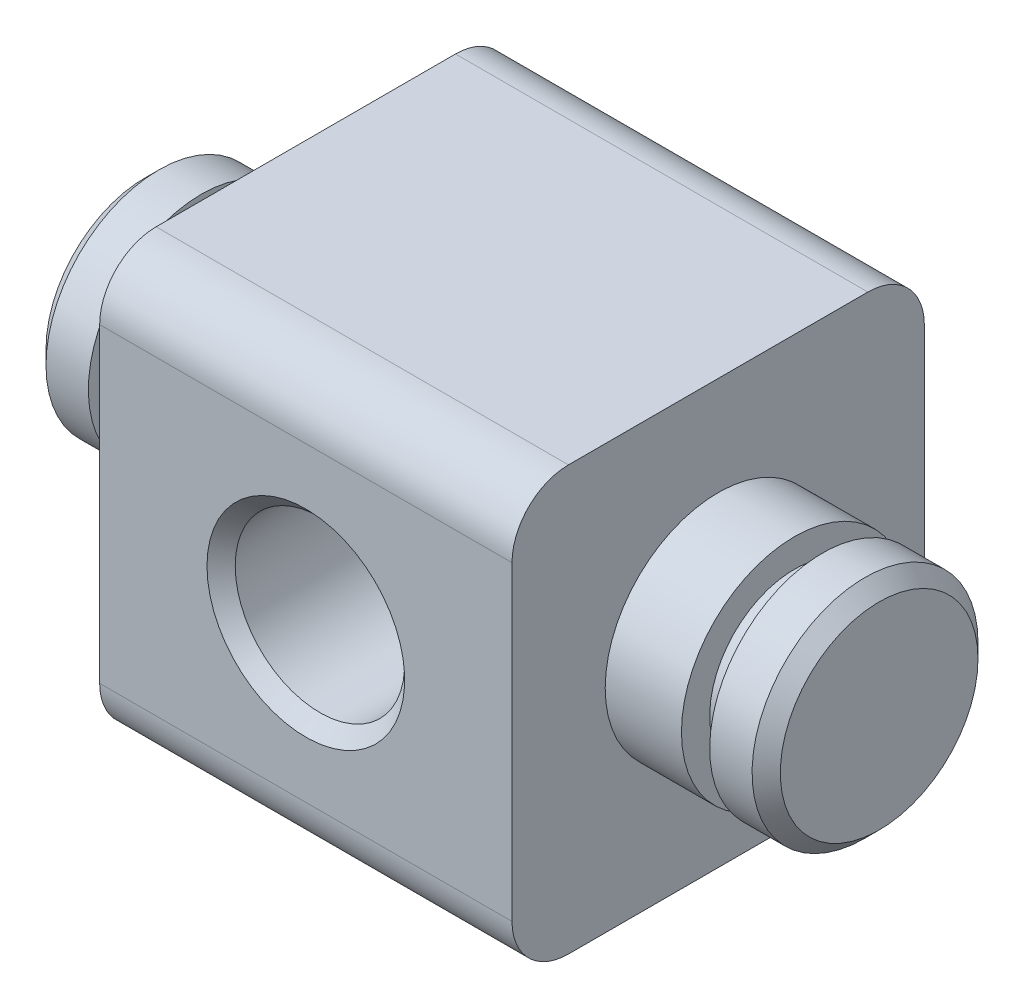
SolidWorks part; units mm, degrees
material "Plain Carbon Steel"
ref_plane "Front Plane" through (0, 0, 0) normal (0, 0, 1) x (1, 0, 0)
ref_plane "Top Plane" through (0, 0, 0) normal (0, 1, 0) x (1, 0, 0)
ref_plane "Right Plane" through (0, 0, 0) normal (1, 0, 0) x (0, 0, -1)
sketch "Sketch1" plane through (0, 0, 0) normal (0, 1, 0) x (1, 0, 0)
  line L1 (7.3, -7.3) -> (-7.3, -7.3)
  line L2 (7.3, -7.3) -> (7.3, 7.3)
  line L3 (7.3, 7.3) -> (-7.3, 7.3)
  line L4 (-7.3, -7.3) -> (-7.3, 7.3)
  line L5 (7.3, -7.3) -> (-7.3, 7.3) construction
  line L6 (7.3, 7.3) -> (-7.3, -7.3) construction
  point P0 (0, 0)
  dimension "D1" = 14.6
extrude "Boss-Extrude1" add sketch "Sketch1" along normal blind 15
sketch "Sketch2" plane through (0, 7.7, -7.3) normal (0, 0, 1) x (1, 0, 0)
  line L0 (-7.3, 7.3) -> (7.3, -7.7) construction
  circle A0 centre (0, -0.2) radius 3
  dimension "D1" = 6
extrude "Cut-Extrude1" cut sketch "Sketch2" along normal through all both and the other way through all from surface contours A0
chamfer "Chamfer1" distance 0.5 angle 45 2 edges at (3, 7.5, -7.3) (3, 7.5, 7.3)
sketch "Sketch3" plane through (-7.3, 0, 0) normal (-1, 0, 0) x (0, 0, 1)
  line L0 (-7.3, 0) -> (7.3, 15) construction
  circle A0 centre (0, 7.5) radius 4
  dimension "D1" = 8
extrude "Boss-Extrude2" add sketch "Sketch3" along normal blind 5.7
sketch "Sketch4" plane through (0, 0, 0) normal (0, 0, 1) x (1, 0, 0)
  line L0 (-13, 7.5) -> (7.3, 7.5) construction
  line L1 (-11, 12.2783) -> (-10, 12.2783)
  line L2 (-11, 12.2783) -> (-11, 10.5)
  line L3 (-11, 10.5) -> (-10, 10.5)
  line L4 (-10, 12.2783) -> (-10, 10.5)
  line L5 (-13, 11.5) -> (-13, 3.5) construction
  line L6 (7.3, 15) -> (7.3, 0) construction
  dimension "D1" = 1
  dimension "D2" = 3
  dimension "D3" = 2
revolve "Cut-Revolve1" cut sketch "Sketch4" angle 360 about L0
chamfer "Chamfer2" distance 0.5 angle 45 1 edges at (-13, 7.5, 4)
mirror "Mirror1" about plane through (0, 0, 0) normal (1, 0, 0) of "Chamfer2", "Cut-Revolve1", "Boss-Extrude2"
fillet "Fillet1" radius 2 4 edges at (0, 0, -7.3) (0, 0, 7.3) (0, 15, -7.3) (0, 15, 7.3)
